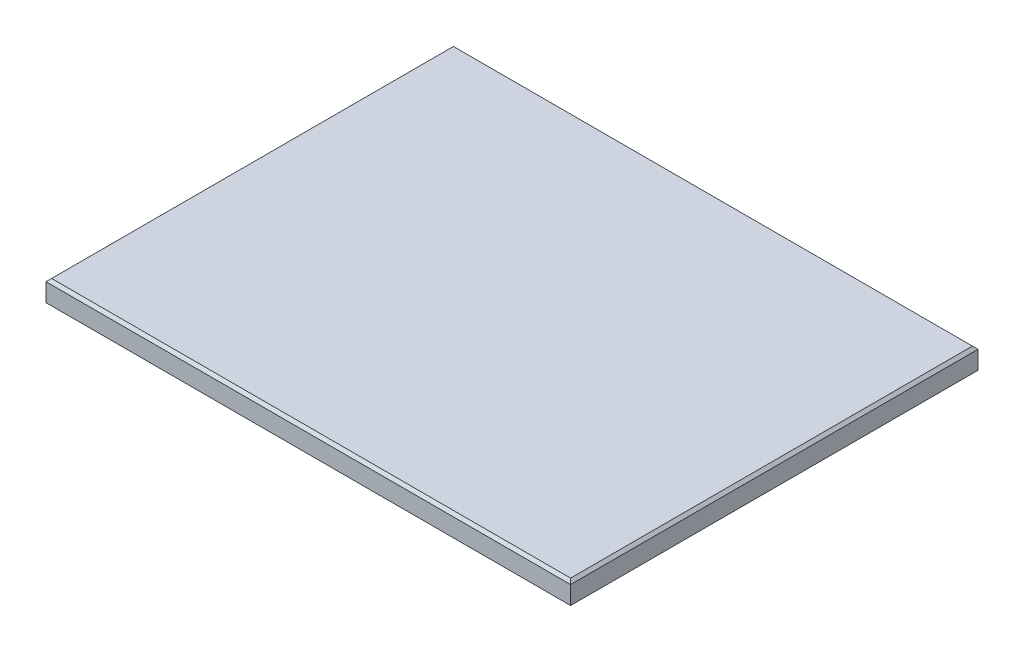
SolidWorks part; units mm, degrees
material "Oak"
ref_plane "Front Plane" through (0, 0, 0) normal (0, 0, 1) x (1, 0, 0)
ref_plane "Top Plane" through (0, 0, 0) normal (0, 1, 0) x (1, 0, 0)
ref_plane "Right Plane" through (0, 0, 0) normal (1, 0, 0) x (0, 0, -1)
sketch "Sketch1" plane through (0, 0, 0) normal (0, 1, 0) x (1, 0, 0)
  line L1 (0, 0) -> (476.25, 0)
  line L2 (0, 0) -> (0, 369.8875)
  line L3 (0, 369.8875) -> (476.25, 369.8875)
  line L4 (476.25, 0) -> (476.25, 369.8875)
  dimension "D1" = 369.8875
  dimension "D2" = 476.25
extrude "Boss-Extrude1" add sketch "Sketch1" along normal blind 19.05
chamfer "Chamfer1" distance 2.54 angle 45 4 edges at (238.125, 19.05, -369.8875) (476.25, 19.05, -184.9437) (238.125, 19.05, 0) (0, 19.05, -184.9437)
